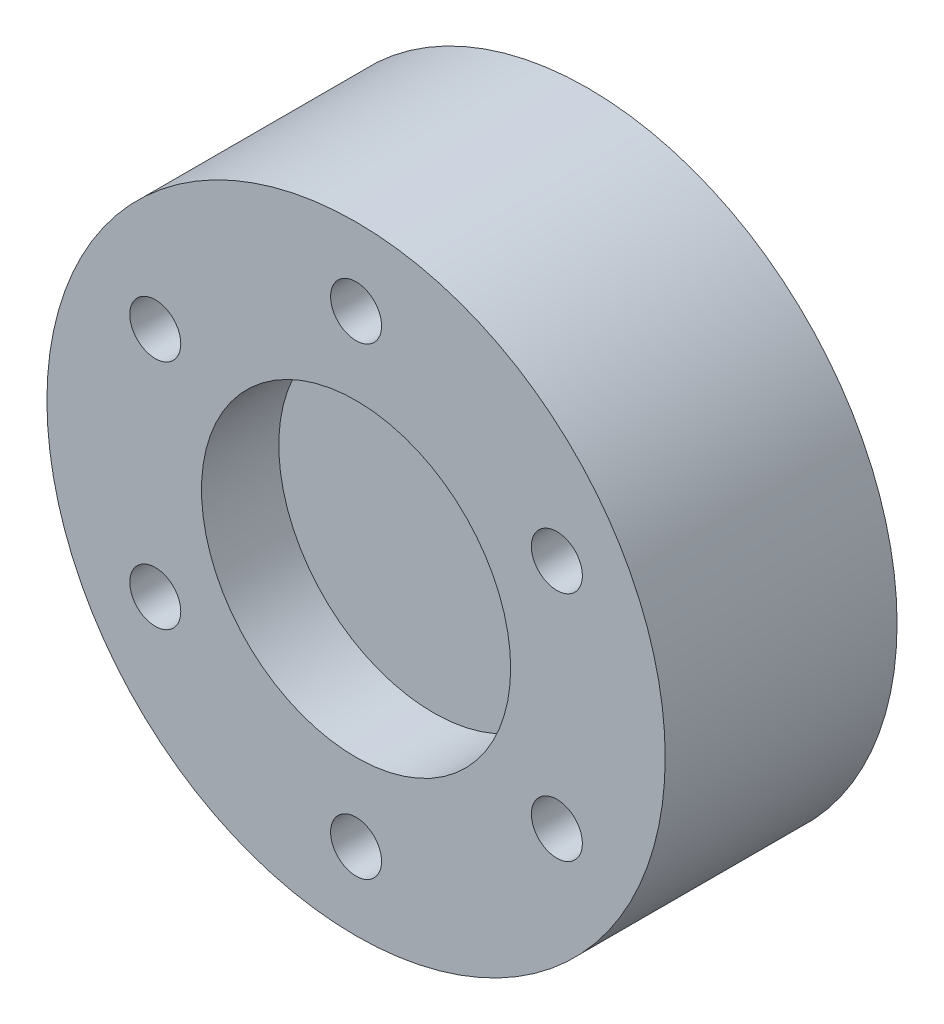
SolidWorks part; units mm, degrees
ref_plane "Front Plane" through (0, 0, 0) normal (0, 0, 1) x (1, 0, 0)
ref_plane "Top Plane" through (0, 0, 0) normal (0, 1, 0) x (1, 0, 0)
ref_plane "Right Plane" through (0, 0, 0) normal (1, 0, 0) x (0, 0, -1)
sketch "Sketch1" plane through (0, 0, 0) normal (0, 0, 1) x (1, 0, 0)
  circle A0 centre (0, 0) radius 20
  dimension "D1" = 40
extrude "Boss-Extrude1" add sketch "Sketch1" along normal blind 15
sketch "Sketch2" plane through (0, 0, 15) normal (0, 0, 1) x (1, 0, 0)
  circle A0 centre (0, 0) radius 10
extrude "Cut-Extrude1" cut sketch "Sketch2" against normal blind 5
hole_wizard "M4x0.7 Tapped Hole1" positions "Sketch3" profile "Sketch4" tap size "M4x0.7" standard "ANSI Metric"
sketch "Sketch3" plane through (0, 0, 15) normal (0, 0, 1) x (1, 0, 0)
  point P0 (0, 15)
  dimension "D1" = 15
sketch "Sketch4" plane through (0, 15, 15) normal (1, 0, 0) x (0, -1, 0)
  line L0 (0, 0) -> (0, 8.0914)
  line L1 (0, 8.0914) -> (1.65, 7.1)
  line L2 (1.65, 7.1) -> (1.65, 0)
  line L5 (1.65, 0) -> (0, 0)
  line L10 (0, 8.0914) -> (-1.65, 7.1) construction
  line L11 (0, -6.35) -> (0, 107.95) construction
  dimension "Tap Drill Dia." = 3.3
  dimension "Tap Drill Depth" = 7.1
  dimension "Drill Angle" = 118
cosmetic thread "Hole Thread1" parameters "D1"=5, "D2"=4
pattern_circular "CirPattern2" count 6 over 360 about axis through (0, 0, 0) along (0, 0, 1) of "M4x0.7 Tapped Hole1"
cosmetic thread "Hole Thread2" parameters "D1"=5, "D2"=4
cosmetic thread "Hole Thread3" parameters "D1"=5, "D2"=4
cosmetic thread "Hole Thread4" parameters "D1"=5, "D2"=4
cosmetic thread "Hole Thread5" parameters "D1"=5, "D2"=4
cosmetic thread "Hole Thread6" parameters "D1"=5, "D2"=4
sketch "Sketch5" plane through (0, 0, 0) normal (0, 0, -1) x (-1, 0, 0)
  circle A0 centre (0, 0) radius 17.5
extrude "Cut-Extrude2" cut sketch "Sketch5" against normal blind 3
